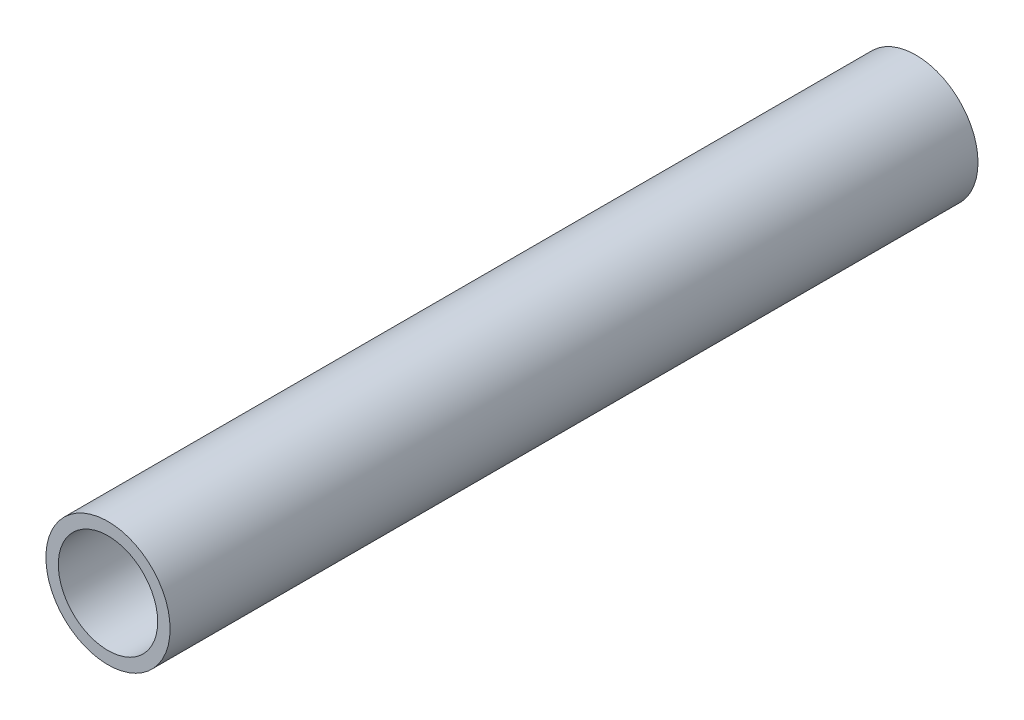
SolidWorks part; units mm, degrees
ref_plane "Front Plane" through (0, 0, 0) normal (0, 0, 1) x (1, 0, 0)
ref_plane "Top Plane" through (0, 0, 0) normal (0, 1, 0) x (1, 0, 0)
ref_plane "Right Plane" through (0, 0, 0) normal (1, 0, 0) x (0, 0, -1)
sketch "Sketch1" plane through (0, 0, 0) normal (0, 0, 1) x (1, 0, 0)
  circle A0 centre (0, 0) radius 1.25
  circle A1 centre (0, 0) radius 1
  dimension "D1" = 2
  dimension "D2" = 2.5
extrude "Boss-Extrude1" add sketch "Sketch1" along normal blind 16.26
equation "\"D1@Boss-Extrude1\" = ( \"D10@Sketch2@indexPIP.SLDPRT\" - \"D7@Sketch2@indexPIP.SLDPRT\" ) * 2'Tube PIP Legth"
